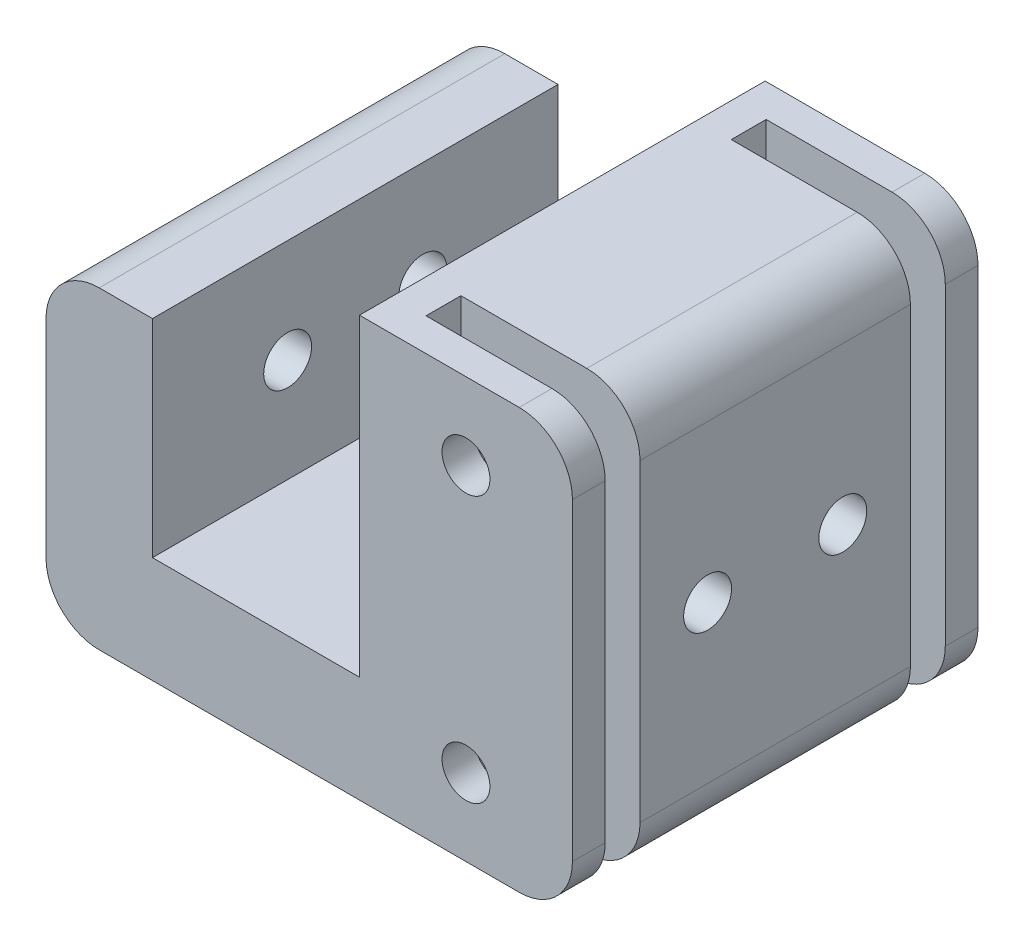
SolidWorks part; units mm, degrees
ref_plane "Front Plane" through (0, 0, 0) normal (0, 0, 1) x (1, 0, 0)
ref_plane "Top Plane" through (0, 0, 0) normal (0, 1, 0) x (1, 0, 0)
ref_plane "Right Plane" through (0, 0, 0) normal (1, 0, 0) x (0, 0, -1)
sketch "Sketch1" plane through (0, 0, 0) normal (0, 0, 1) x (1, 0, 0)
  line L0 (-9.725, 9.725) -> (-14.725, 9.725)
  line L1 (-9.725, -9.725) -> (9.725, -9.725)
  line L2 (-9.725, -9.725) -> (-9.725, 9.725)
  line L3 (-9.725, 9.725) -> (9.725, 9.725) construction
  line L4 (9.725, -9.725) -> (9.725, 9.725)
  line L5 (-9.725, -9.725) -> (9.725, 9.725) construction
  line L6 (-9.725, 9.725) -> (9.725, -9.725) construction
  line L7 (-19.725, 4.725) -> (-19.725, -14.725)
  line L8 (-14.725, -19.725) -> (24.725, -19.725)
  line L9 (29.725, -14.725) -> (29.725, 14.725)
  line L11 (19.725, -12.5) -> (19.725, 12.5) construction
  line L12 (9.725, 9.725) -> (9.725, 19.725)
  line L13 (9.725, 19.725) -> (24.725, 19.725)
  circle A0 centre (19.725, 12.5) radius 2.25
  circle A1 centre (19.725, -12.5) radius 2.25
  arc A3 (24.725, -19.725) -> (29.725, -14.725) centre (24.725, -14.725) ccw
  arc A4 (-19.725, -14.725) -> (-14.725, -19.725) centre (-14.725, -14.725) ccw
  arc A5 (-14.725, 9.725) -> (-19.725, 4.725) centre (-14.725, 4.725) ccw
  arc A6 (24.725, 19.725) -> (29.725, 14.725) centre (24.725, 14.725) cw
  point P0 (0, 0)
  point P11 (19.725, 0)
  point P16 (29.725, 0)
  point P26 (-19.725, 9.725)
  dimension "D5" = 4.5
  dimension "D7" = 10
  dimension "D9" = 5
  dimension "D1" = 19.45
  dimension "D2" = 10
  dimension "D3" = 10
  dimension "D4" = 20
  dimension "D6" = 25
  dimension "D8" = 10
extrude "Boss-Extrude1" add sketch "Sketch1" along normal mid plane 38.1
sketch "Sketch2" plane through (0, 0, 0) normal (0, 1, 0) x (1, 0, 0)
  line L0 (29.725, -19.05) -> (29.725, 19.05) construction
  line L1 (29.725, 15.975) -> (12.9, 15.975)
  line L2 (29.725, 15.975) -> (29.725, 12.7)
  line L3 (29.725, 12.7) -> (12.9, 12.7)
  line L4 (12.9, 15.975) -> (12.9, 12.7)
  line L5 (12.9, -12.7) -> (12.9, 12.7) construction
  line L6 (29.725, -12.7) -> (12.9, -12.7)
  line L7 (29.725, -12.7) -> (29.725, -15.975)
  line L8 (29.725, -15.975) -> (12.9, -15.975)
  line L9 (12.9, -12.7) -> (12.9, -15.975)
  line L12 (9.725, -19.05) -> (9.725, 19.05) construction
  point P10 (12.9, 0)
  dimension "D1" = 3.275
  dimension "D2" = 25.4
  dimension "D3" = 3.175
extrude "Cut-Extrude1" cut sketch "Sketch2" against normal through all both and the other way through all
sketch "Sketch4" plane through (0, 0, 0) normal (1, 0, 0) x (0, 0, -1)
  line L0 (-6.35, 0) -> (6.35, 0) construction
  circle A0 centre (-6.35, 0) radius 2.25
  circle A1 centre (6.35, 0) radius 2.25
  point P4 (0, 0)
  dimension "D1" = 4.5
  dimension "D2" = 12.7
extrude "Cut-Extrude2" cut sketch "Sketch4" against normal through all both and the other way through all
